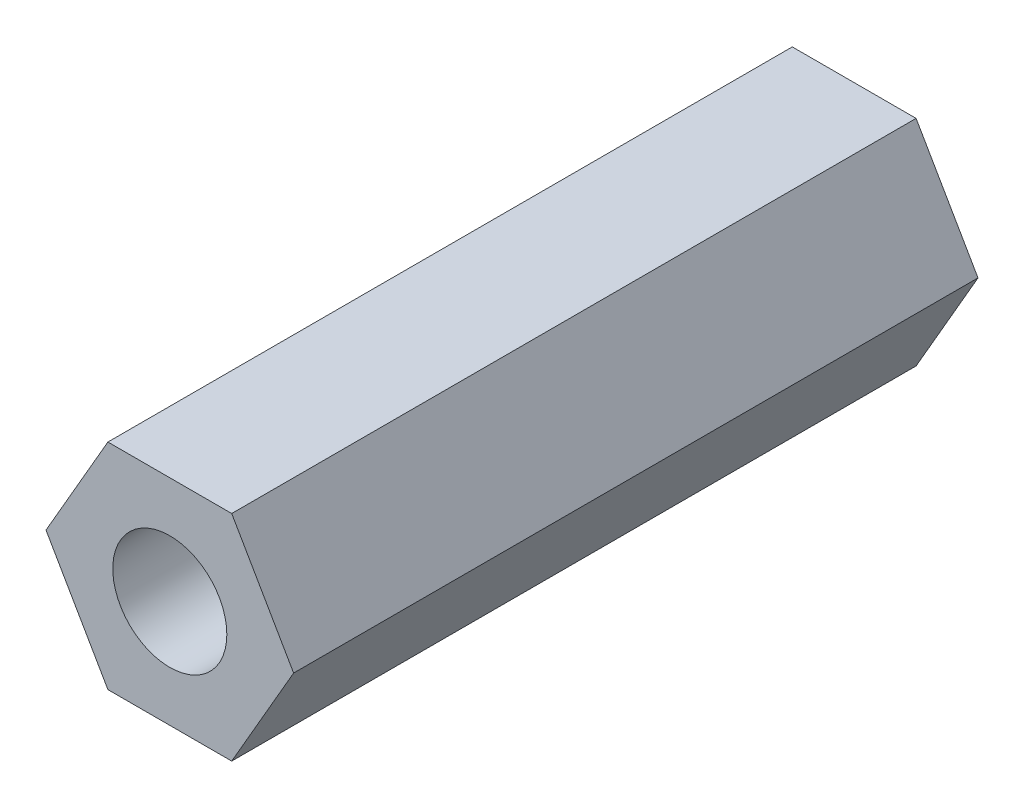
SolidWorks part; units mm, degrees
material "AISI 304"
ref_plane "前视基准面" through (0, 0, 0) normal (0, 0, 1) x (1, 0, 0)
ref_plane "上视基准面" through (0, 0, 0) normal (0, 1, 0) x (1, 0, 0)
ref_plane "右视基准面" through (0, 0, 0) normal (1, 0, 0) x (0, 0, -1)
sketch "草图1" plane through (0, 0, 0) normal (0, 0, 1) x (1, 0, 0)
  line L1 (1.3568, 2.35) -> (-1.3568, 2.35)
  line L2 (-1.3568, 2.35) -> (-2.7135, 0)
  line L3 (-2.7135, 0) -> (-1.3568, -2.35)
  line L4 (-1.3568, -2.35) -> (1.3568, -2.35)
  line L5 (1.3568, -2.35) -> (2.7135, 0)
  line L6 (2.7135, 0) -> (1.3568, 2.35)
  circle A0 centre (0, 0) radius 2.35 construction
  dimension "D1" = 4.7
extrude "凸台-拉伸1" add sketch "草图1" along normal mid plane 15
hole_wizard "螺纹孔" positions "草图2" profile "草图3" tap size "M2" standard "GB"
sketch "草图2" plane through (0, 0, 7.5) normal (0, 0, 1) x (1, 0, 0)
  point P0 (0, 0)
sketch "草图3" plane through (0, 0, 7.5) normal (1, 0, 0) x (0, -1, 0)
  line L0 (0, 0) -> (0, 8.7511)
  line L1 (0, 8.7511) -> (1.25, 8)
  line L2 (1.25, 8) -> (1.25, 0)
  line L5 (1.25, 0) -> (0, 0)
  line L10 (0, 8.7511) -> (-1.25, 8) construction
  line L11 (0, -6.35) -> (0, 107.95) construction
  dimension "螺纹孔钻头直径" = 2.5
  dimension "螺纹孔钻头深度" = 8
  dimension "导头角度" = 118
cosmetic thread "孔螺蚊线1" parameters "D1"=6, "D2"=2.9
mirror "镜向1" about plane through (0, 0, 0) normal (0, 0, 1) of "螺纹孔"
cosmetic thread "孔螺蚊线2" parameters "D1"=6, "D2"=2.9
